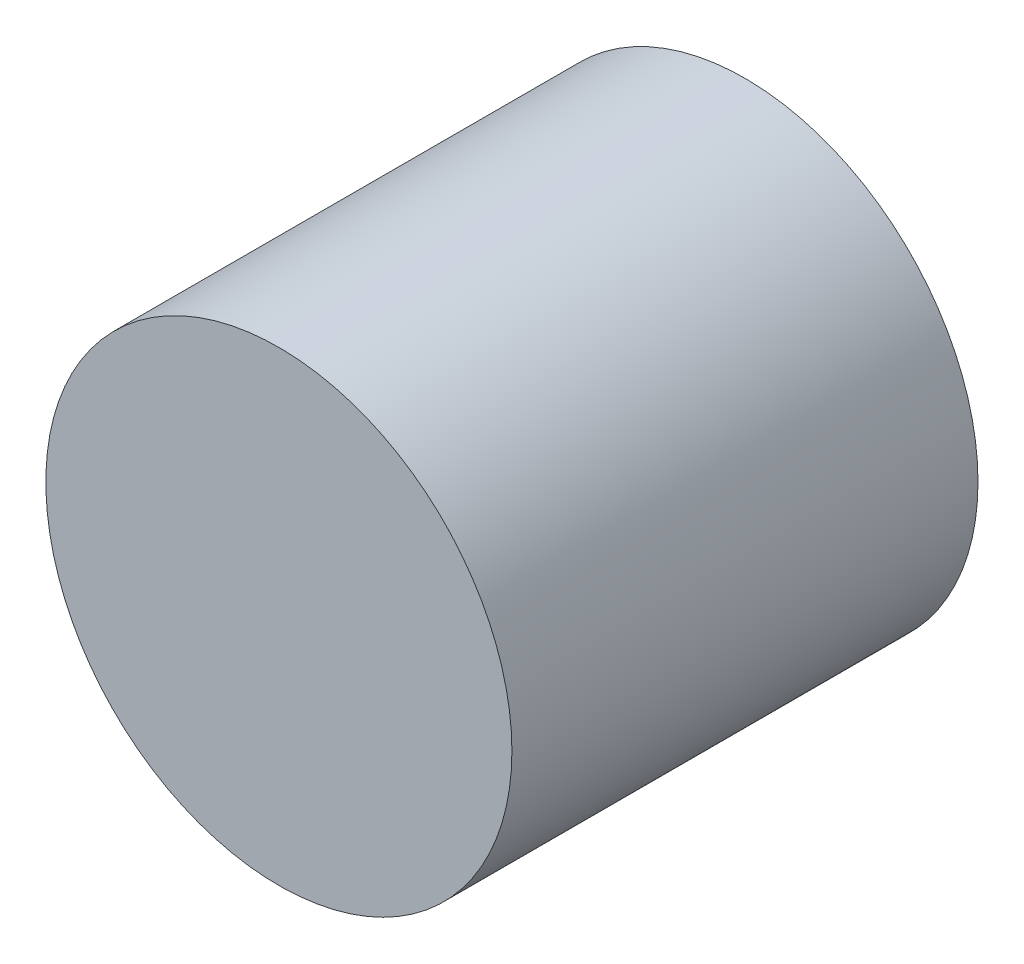
SolidWorks part; units mm, degrees
ref_plane "Front Plane" through (0, 0, 0) normal (0, 0, 1) x (1, 0, 0)
ref_plane "Top Plane" through (0, 0, 0) normal (0, 1, 0) x (1, 0, 0)
ref_plane "Right Plane" through (0, 0, 0) normal (1, 0, 0) x (0, 0, -1)
sketch "Sketch1" plane through (0, 0, 0) normal (0, 0, 1) x (1, 0, 0)
  circle A0 centre (0, 0) radius 3.2
extrude "Boss-Extrude1" add sketch "Sketch1" along normal blind 6.4
